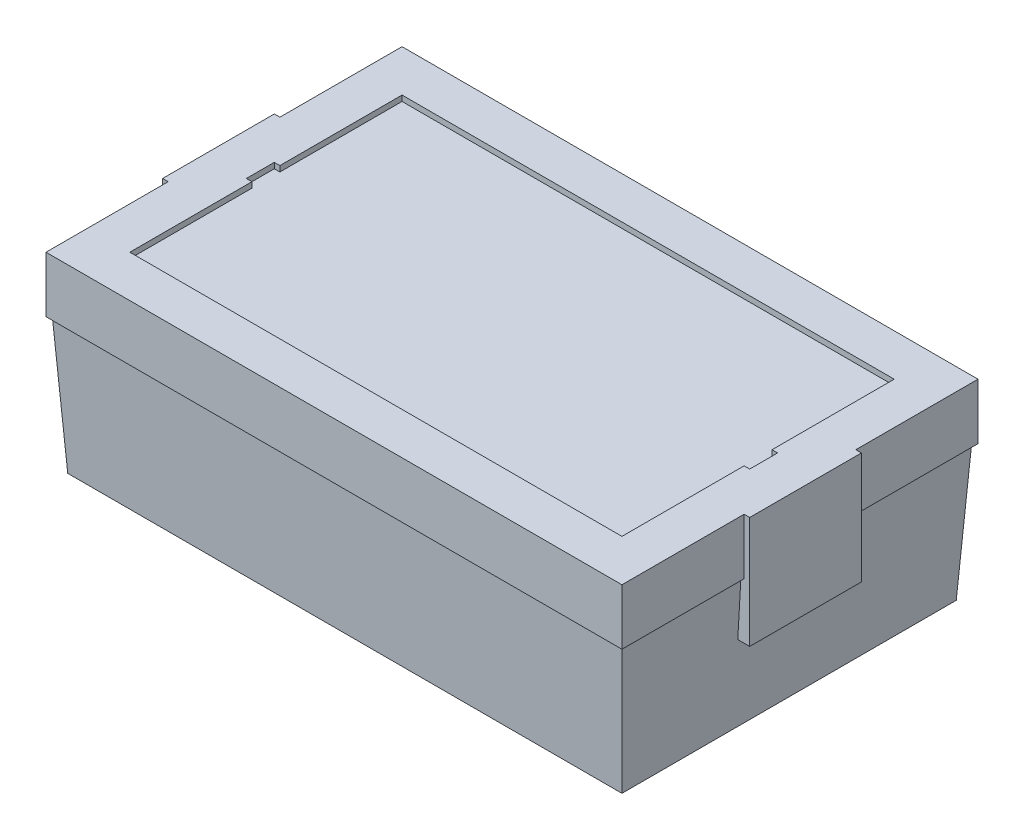
SolidWorks part; units mm, degrees
ref_plane "Front Plane" through (0, 0, 0) normal (0, 0, 1) x (1, 0, 0)
ref_plane "Top Plane" through (0, 0, 0) normal (0, 1, 0) x (1, 0, 0)
ref_plane "Right Plane" through (0, 0, 0) normal (1, 0, 0) x (0, 0, -1)
sketch "Sketch1" plane through (0, 0, 0) normal (0, 1, 0) x (1, 0, 0)
  line L1 (-109.22, -69.85) -> (109.22, -69.85)
  line L2 (-109.22, -69.85) -> (-109.22, 69.85)
  line L3 (-109.22, 69.85) -> (109.22, 69.85)
  line L4 (109.22, -69.85) -> (109.22, 69.85)
  line L5 (-109.22, -69.85) -> (109.22, 69.85) construction
  line L6 (-109.22, 69.85) -> (109.22, -69.85) construction
  point P0 (0, 0)
  dimension "D1" = 218.44
  dimension "D2" = 139.7
extrude "Boss-Extrude1" add sketch "Sketch1" along normal mid plane 68.58
sketch "Sketch2" plane through (0, -34.29, 0) normal (0, -1, 0) x (1, 0, 0)
  line L8 (99.22, -59.85) -> (99.22, 59.85)
  line L9 (99.22, 59.85) -> (-99.22, 59.85)
  line L10 (-99.22, 59.85) -> (-99.22, -59.85)
  line L11 (-99.22, -59.85) -> (99.22, -59.85)
  line L12 (99.22, -59.85) -> (99.22, 59.85)
  line L13 (99.22, 59.85) -> (-99.22, 59.85)
  line L14 (-99.22, 59.85) -> (-99.22, -59.85)
  line L15 (-99.22, -59.85) -> (99.22, -59.85)
  line L28 (119.22, -79.85) -> (119.22, 79.85)
  line L29 (119.22, 79.85) -> (-119.22, 79.85)
  line L30 (-119.22, 79.85) -> (-119.22, -79.85)
  line L31 (-119.22, -79.85) -> (119.22, -79.85)
  line L32 (119.22, -79.85) -> (119.22, 79.85)
  line L33 (119.22, 79.85) -> (-119.22, 79.85)
  line L34 (-119.22, 79.85) -> (-119.22, -79.85)
  line L35 (-119.22, -79.85) -> (119.22, -79.85)
  dimension "D1" = 10
  dimension "D2" = 10
extrude "Cut-Extrude1" cut sketch "Sketch2" against normal blind 172.72 draft 3.25
sketch "Sketch3" plane through (0, 34.29, 0) normal (0, 1, 0) x (1, 0, 0)
  line L4 (103.1143, 63.7443) -> (-103.1143, 63.7443)
  line L5 (-103.1143, 63.7443) -> (-103.1143, -63.7443)
  line L6 (-103.1143, -63.7443) -> (103.1143, -63.7443)
  line L7 (103.1143, -63.7443) -> (103.1143, 63.7443)
  line L8 (103.1143, 63.7443) -> (-103.1143, 63.7443)
  line L9 (-103.1143, 63.7443) -> (-103.1143, -63.7443)
  line L10 (-103.1143, -63.7443) -> (103.1143, -63.7443)
  line L11 (103.1143, -63.7443) -> (103.1143, 63.7443)
  dimension "D1" = 0
extrude "Boss-Extrude2" add sketch "Sketch3" against normal blind 20
sketch "Sketch4" plane through (103.1143, 0, 0) normal (1, 0, 0) x (0, 0, -1)
  line L0 (-63.7443, 14.29) -> (63.7443, 14.29) construction
  line L1 (-20, -5.71) -> (20, -5.71)
  line L2 (-20, -5.71) -> (-20, 34.29)
  line L3 (-20, 34.29) -> (20, 34.29)
  line L4 (20, -5.71) -> (20, 34.29)
  line L5 (-20, -5.71) -> (20, 34.29) construction
  line L6 (-20, 34.29) -> (20, -5.71) construction
  line L7 (63.7443, 34.29) -> (-63.7443, 34.29) construction
  point P0 (0, 14.29)
  dimension "D1" = 40
extrude "Boss-Extrude3" add sketch "Sketch4" against normal blind 20 and the other way blind 2
mirror "Mirror1" about plane through (0, 0, 0) normal (1, 0, 0) of "Boss-Extrude3"
sketch "Sketch5" plane through (0, 34.29, 0) normal (0, 1, 0) x (1, 0, 0)
  line L24 (-88.1143, 48.7443) -> (-88.1143, 5)
  line L25 (-88.1143, -48.7443) -> (88.1143, -48.7443)
  line L26 (88.1143, -48.7443) -> (88.1143, -5)
  line L27 (88.1143, 48.7443) -> (-88.1143, 48.7443)
  line L28 (-88.1143, 48.7443) -> (-88.1143, 5)
  line L29 (-88.1143, -48.7443) -> (88.1143, -48.7443)
  line L30 (88.1143, -48.7443) -> (88.1143, -5)
  line L31 (88.1143, 48.7443) -> (-88.1143, 48.7443)
  line L32 (-88.1143, 5) -> (-90.1143, 5)
  line L33 (-88.1143, 5) -> (-90.1143, 5)
  line L34 (-90.1143, 5) -> (-90.1143, -5)
  line L35 (-90.1143, 5) -> (-90.1143, -5)
  line L36 (-90.1143, -5) -> (-88.1143, -5)
  line L37 (-90.1143, -5) -> (-88.1143, -5)
  line L38 (-88.1143, -5) -> (-88.1143, -48.7443)
  line L39 (-88.1143, -5) -> (-88.1143, -48.7443)
  line L40 (88.1143, -5) -> (90.1143, -5)
  line L41 (88.1143, -5) -> (90.1143, -5)
  line L42 (90.1143, -5) -> (90.1143, 5)
  line L43 (90.1143, -5) -> (90.1143, 5)
  line L44 (90.1143, 5) -> (88.1143, 5)
  line L45 (90.1143, 5) -> (88.1143, 5)
  line L46 (88.1143, 5) -> (88.1143, 48.7443)
  line L47 (88.1143, 5) -> (88.1143, 48.7443)
  dimension "D1" = 15
extrude "Cut-Extrude2" cut sketch "Sketch5" against normal blind 2
